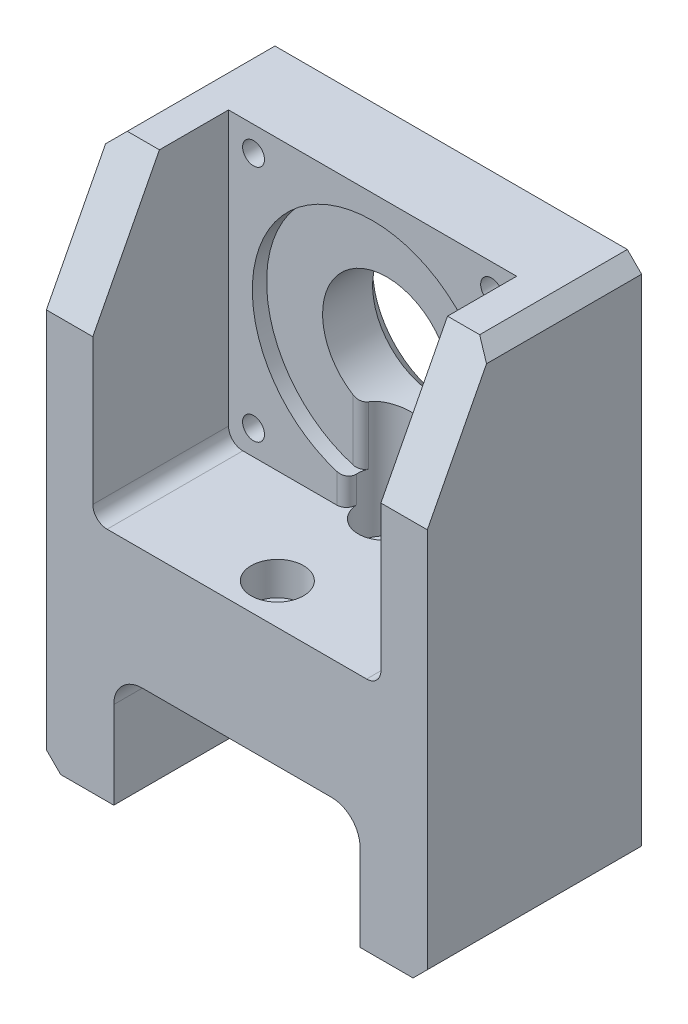
SolidWorks part; units mm, degrees
ref_plane "Front Plane" through (0, 0, 0) normal (0, 0, 1) x (1, 0, 0)
ref_plane "Top Plane" through (0, 0, 0) normal (0, 1, 0) x (1, 0, 0)
ref_plane "Right Plane" through (0, 0, 0) normal (1, 0, 0) x (0, 0, -1)
sketch "Sketch1" plane through (0, 0, 0) normal (0, 0, 1) x (1, 0, 0)
  line L0 (0, -24.75) -> (0, 0) construction
  line L1 (40, -79.75) -> (25.85, -79.75)
  line L2 (40, -79.75) -> (40, 30.25)
  line L3 (40, 30.25) -> (-40, 30.25)
  line L4 (-40, -79.75) -> (-40, 30.25)
  line L5 (40, -79.75) -> (-40, 30.25) construction
  line L6 (40, 30.25) -> (-40, -79.75) construction
  line L7 (0, -67.6) -> (0, -24.75) construction
  line L8 (25.85, -55.45) -> (-25.85, -55.45)
  line L9 (25.85, -55.45) -> (25.85, -79.75)
  line L11 (-25.85, -55.45) -> (-25.85, -79.75)
  line L12 (25.85, -55.45) -> (-25.85, -79.75) construction
  line L13 (25.85, -79.75) -> (-25.85, -55.45) construction
  line L14 (-25.85, -79.75) -> (-40, -79.75)
  circle A0 centre (0, 0) radius 13.5
  point P0 (0, -24.75)
  point P9 (0, -67.6)
  dimension "D1" = 27
  dimension "D2" = 80
  dimension "D3" = 110
  dimension "D4" = 55.45
  dimension "D5" = 51.7
  dimension "D6" = 30.25
extrude "Boss-Extrude1" add sketch "Sketch1" along normal mid plane 45
sketch "Sketch2" plane through (0, 0, 22.5) normal (0, 0, 1) x (1, 0, 0)
  line L0 (40, 30.25) -> (-40, 30.25) construction
  line L1 (30.25, -30.25) -> (-30.25, -30.25)
  line L2 (30.25, -30.25) -> (30.25, 30.25)
  line L3 (30.25, 30.25) -> (-30.25, 30.25)
  line L4 (-30.25, -30.25) -> (-30.25, 30.25)
  line L5 (30.25, -30.25) -> (-30.25, 30.25) construction
  line L6 (30.25, 30.25) -> (-30.25, -30.25) construction
  point P0 (0, 0)
extrude "Cut-Extrude1" cut sketch "Sketch2" against normal blind 28.5
sketch "Sketch3" plane through (0, 0, -6) normal (0, 0, 1) x (1, 0, 0)
  circle A0 centre (0, 0) radius 25.25
  dimension "D1" = 50.5
extrude "Cut-Extrude2" cut sketch "Sketch3" against normal blind 3
sketch "Sketch4" plane through (0, 0, -6) normal (0, 0, 1) x (1, 0, 0)
  line L1 (25, -25) -> (-25, -25) construction
  line L2 (25, -25) -> (25, 25) construction
  line L3 (25, 25) -> (-25, 25) construction
  line L4 (-25, -25) -> (-25, 25) construction
  line L5 (25, -25) -> (-25, 25) construction
  line L6 (25, 25) -> (-25, -25) construction
  circle A0 centre (-25, 25) radius 2.3
  circle A1 centre (25, 25) radius 2.3
  circle A2 centre (25, -25) radius 2.3
  circle A3 centre (-25, -25) radius 2.3
  point P0 (0, 0)
  dimension "D2" = 4.6
  dimension "D1" = 50
extrude "Cut-Extrude3" cut sketch "Sketch4" against normal through all both and the other way through all
chamfer "Chamfer1" distance 3 angle 45 1 edges at (13.5, 0, -22.5)
sketch "Sketch5" plane through (0, 0, 0) normal (0, 1, 0) x (1, 0, 0)
  line L0 (0, 8.5) -> (0, -14) construction
  line L1 (-30.25, -22.5) -> (30.25, -22.5) construction
  circle A0 centre (0, 8.5) radius 3.05
  circle A1 centre (0, -14) radius 3.05
  dimension "D1" = 6.1
  dimension "D2" = 22.5
  dimension "D3" = 8.5
extrude "Cut-Extrude4" cut sketch "Sketch5" against normal through all
sketch "Sketch6" plane through (0, 0, 0) normal (0, 1, 0) x (1, 0, 0)
  circle A0 centre (0, -14) radius 5.5
  circle A1 centre (0, 8.5) radius 5.5
  dimension "D1" = 11
extrude "Cut-Extrude5" cut sketch "Sketch6" against normal offset from surface (37.25 mm away) 7 up to face at (0, -30.25, 10.95) offset beyond the face yes
fillet "Fillet1" radius 3 2 edges at (30.25, -30.25, 8.25) (-30.25, -30.25, 8.25)
fillet "Fillet2" radius 6 2 edges at (-25.85, -55.45, 0) (25.85, -55.45, 0)
fillet "Fillet3" radius 2 4 edges at (5.4772, -18.4939, -9) (-5.4772, -18.4939, -9) (4.899, -27.5101, -6) (-4.899, -27.5101, -6)
chamfer "Chamfer2" distance 3 angle 45 4 edges at (-40, -79.75, 0) (40, -79.75, 0) (-40, 30.25, 0) (40, 30.25, 0)
sketch "Sketch7" plane through (40, 0, 0) normal (1, 0, 0) x (0, 0, -1)
  line L0 (-8.5125, 30.25) -> (-22.5, 3.2603)
  line L1 (-22.5, 30.25) -> (22.5, 30.25) construction
  line L2 (-22.5, -76.75) -> (-22.5, 27.25) construction
  line L3 (-22.5, 3.2603) -> (-22.5, 30.25)
  line L4 (-22.5, 30.25) -> (-8.5125, 30.25)
extrude "Cut-Extrude6" cut sketch "Sketch7" against normal through all both and the other way through all
